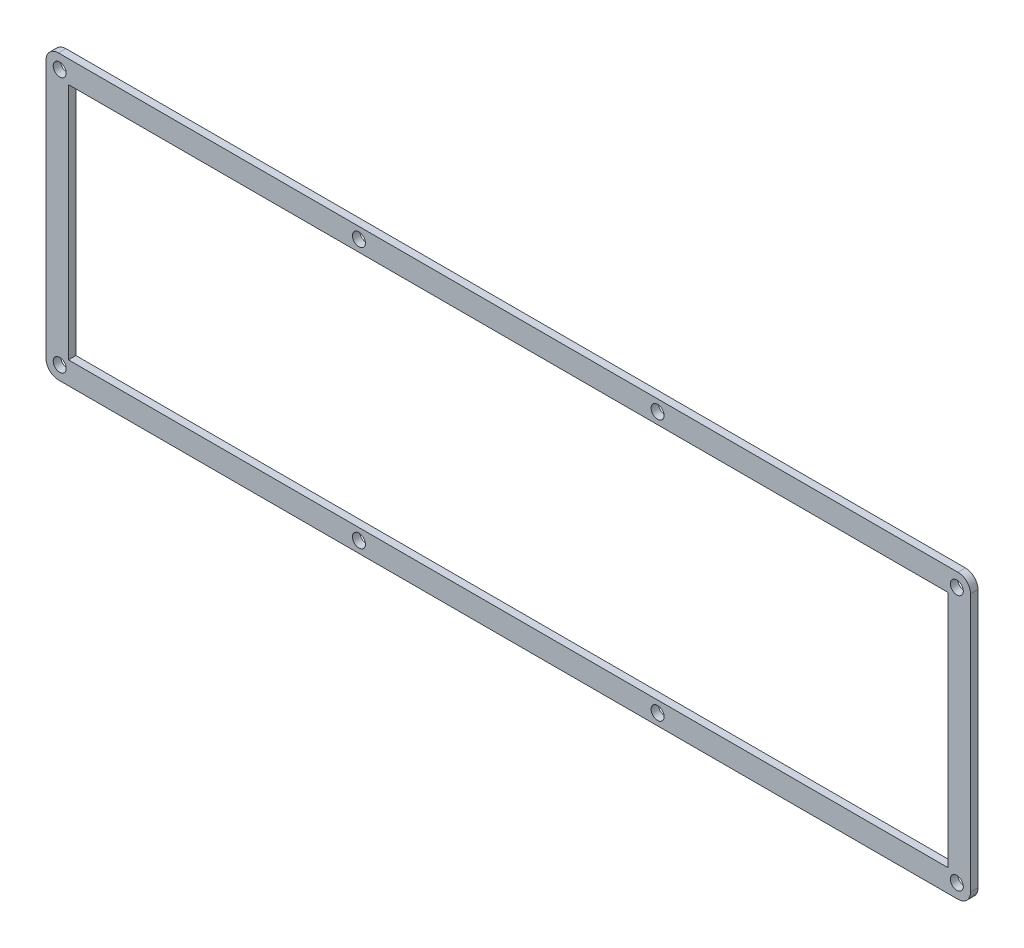
SolidWorks part; units mm, degrees
ref_plane "Front Plane" through (0, 0, 0) normal (0, 0, 1) x (1, 0, 0)
ref_plane "Top Plane" through (0, 0, 0) normal (0, 1, 0) x (1, 0, 0)
ref_plane "Right Plane" through (0, 0, 0) normal (1, 0, 0) x (0, 0, -1)
sketch "Model" plane through (0, 0, 0) normal (0, 0, 1) x (1, 0, 0)
  line L0 (0, 108.6) -> (0, 5)
  line L1 (9, 104.6) -> (9, 9)
  line L2 (365.775, 0) -> (5, 0)
  line L3 (361.775, 9) -> (9, 9)
  line L4 (370.775, 108.6) -> (370.775, 5)
  line L5 (361.775, 104.6) -> (361.775, 9)
  line L6 (365.775, 113.6) -> (5, 113.6)
  line L7 (361.775, 104.6) -> (9, 104.6)
  arc A0 (365.775, 0) -> (370.775, 5) centre (365.775, 5) ccw
  arc A1 (370.775, 108.6) -> (365.775, 113.6) centre (365.775, 108.6) ccw
  arc A2 (0, 5) -> (5, 0) centre (5, 5) ccw
  circle A3 centre (5.5, 108.1) radius 2.6
  circle A4 centre (5.5, 5.5) radius 2.6
  circle A5 centre (365.275, 5.5) radius 2.6
  circle A6 centre (365.275, 108.1) radius 2.6
  arc A7 (5, 113.6) -> (0, 108.6) centre (5, 108.6) ccw
  circle A8 centre (125.5, 4.5) radius 2.6
  circle A9 centre (245.275, 4.5) radius 2.6
  circle A10 centre (125.5, 109.1) radius 2.6
  circle A11 centre (245.275, 109.1) radius 2.6
  dimension "D1" = 5.2
  dimension "D2" = 5.2
extrude "Boss-Extrude1" add sketch "Model" along normal blind 3
